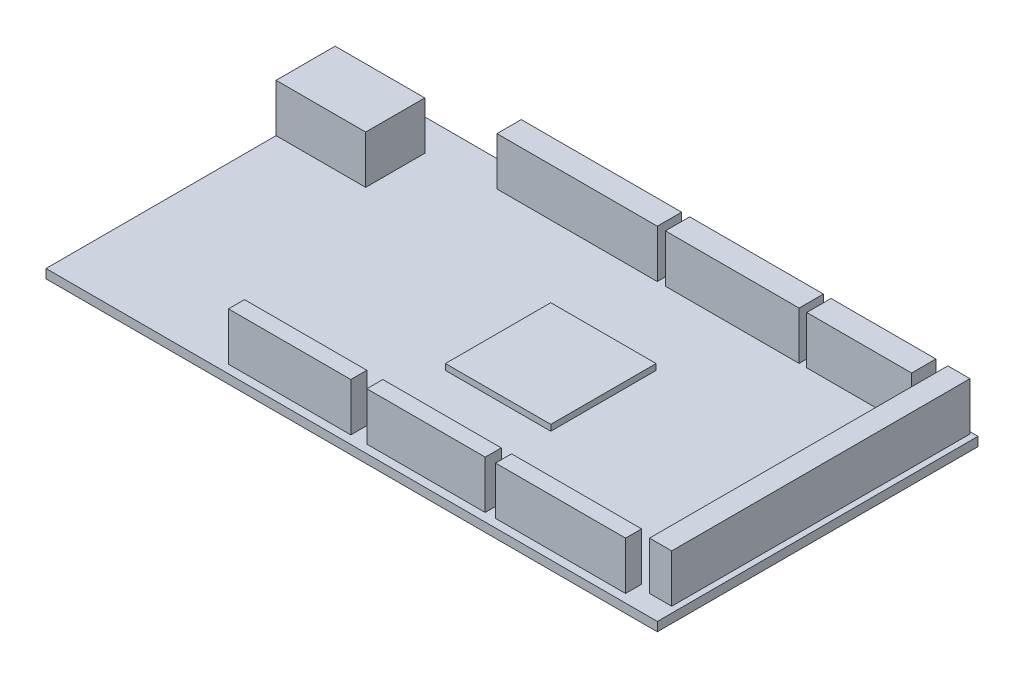
SolidWorks part; units mm, degrees
material "Sheet Moulding Compound"
ref_plane "Front Plane" through (0, 0, 0) normal (0, 0, 1) x (1, 0, 0)
ref_plane "Top Plane" through (0, 0, 0) normal (0, 1, 0) x (1, 0, 0)
ref_plane "Right Plane" through (0, 0, 0) normal (1, 0, 0) x (0, 0, -1)
sketch "Sketch1" plane through (0, 0, 0) normal (0, 1, 0) x (1, 0, 0)
  line L1 (0, 0) -> (102, 0)
  line L2 (0, 0) -> (0, 53.5)
  line L3 (0, 53.5) -> (102, 53.5)
  line L4 (102, 0) -> (102, 53.5)
  dimension "D1" = 53.5
  dimension "D2" = 102
extrude "Boss-Extrude1" add sketch "Sketch1" along normal blind 1.5
sketch "Sketch2" plane through (0, 1.5, 0) normal (0, 1, 0) x (-1, 0, 0)
  line L0 (0, -53.5) -> (0, 0) construction
  line L1 (0, -48.243) -> (-14.9523, -48.243)
  line L2 (0, -48.243) -> (0, -38.3857)
  line L3 (0, -38.3857) -> (-14.9523, -38.3857)
  line L4 (-14.9523, -48.243) -> (-14.9523, -38.3857)
extrude "Boss-Extrude2" add sketch "Sketch2" along normal blind 8
sketch "Sketch3" plane through (0, 1.5, 0) normal (0, 1, 0) x (-1, 0, 0)
  line L1 (-26.1319, -53.1633) -> (-52.8832, -53.1633)
  line L2 (-26.1319, -53.1633) -> (-26.1319, -49.1071)
  line L3 (-26.1319, -49.1071) -> (-52.8832, -49.1071)
  line L4 (-52.8832, -53.1633) -> (-52.8832, -49.1071)
  line L5 (-54.2352, -53.1633) -> (-76.5441, -53.1633)
  line L6 (-54.2352, -53.1633) -> (-54.2352, -49.1071)
  line L7 (-54.2352, -49.1071) -> (-76.5441, -49.1071)
  line L8 (-76.5441, -53.1633) -> (-76.5441, -49.1071)
  line L9 (-77.8143, -49.1071) -> (-95.3118, -49.1071)
  line L10 (-77.8143, -49.1071) -> (-77.8143, -53.1633)
  line L11 (-77.8143, -53.1633) -> (-95.3118, -53.1633)
  line L12 (-95.3118, -49.1071) -> (-95.3118, -53.1633)
  line L13 (-97.3077, -53.1633) -> (-101.0019, -53.1633)
  line L14 (-97.3077, -53.1633) -> (-97.3077, -3.3911)
  line L15 (-97.3077, -3.3911) -> (-101.0019, -3.3911)
  line L16 (-101.0019, -53.1633) -> (-101.0019, -3.3911)
  line L17 (-95.3118, -1.3873) -> (-73.6161, -1.3873)
  line L18 (-95.3118, -1.3873) -> (-95.3118, -4.0591)
  line L19 (-95.3118, -4.0591) -> (-73.6161, -4.0591)
  line L20 (-73.6161, -1.3873) -> (-73.6161, -4.0591)
  line L21 (-71.8986, -4.0591) -> (-52.1464, -4.0591)
  line L22 (-71.8986, -4.0591) -> (-71.8986, -1.3873)
  line L23 (-71.8986, -1.3873) -> (-52.1464, -1.3873)
  line L24 (-52.1464, -4.0591) -> (-52.1464, -1.3873)
  line L25 (-49.4747, -1.3873) -> (-29.0546, -1.3873)
  line L26 (-49.4747, -1.3873) -> (-49.4747, -4.0591)
  line L27 (-49.4747, -4.0591) -> (-29.0546, -4.0591)
  line L28 (-29.0546, -1.3873) -> (-29.0546, -4.0591)
extrude "Boss-Extrude3" add sketch "Sketch3" along normal blind 8
sketch "Sketch4" plane through (0, 1.5, 0) normal (0, 1, 0) x (-1, 0, 0)
  line L1 (-48.0544, -36.1661) -> (-65.6311, -36.1661)
  line L2 (-48.0544, -36.1661) -> (-48.0544, -18.5894)
  line L3 (-48.0544, -18.5894) -> (-65.6311, -18.5894)
  line L4 (-65.6311, -36.1661) -> (-65.6311, -18.5894)
extrude "Boss-Extrude4" add sketch "Sketch4" along normal blind 1
